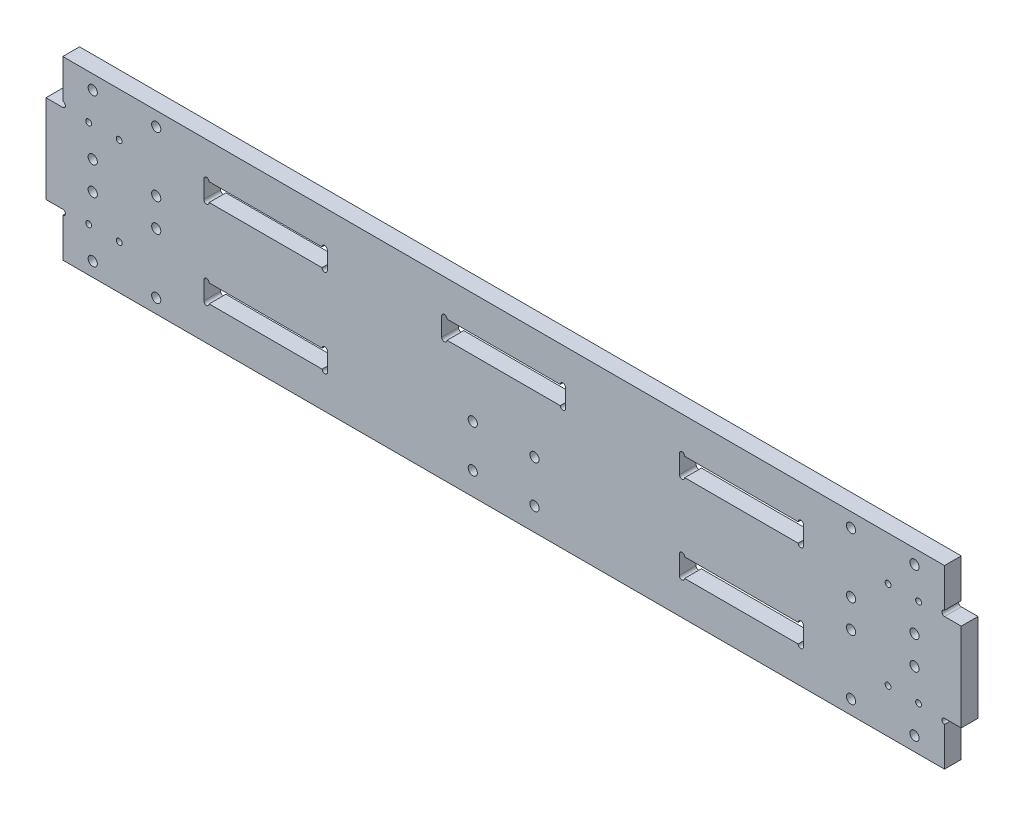
SolidWorks part; units mm, degrees
ref_plane "Front Plane" through (0, 0, 0) normal (0, 0, 1) x (1, 0, 0)
ref_plane "Top Plane" through (0, 0, 0) normal (0, 1, 0) x (1, 0, 0)
ref_plane "Right Plane" through (0, 0, 0) normal (1, 0, 0) x (0, 0, -1)
sketch "Sketch1" plane through (0, 0, 0) normal (0, 0, 1) x (1, 0, 0)
  line L0 (-250, -25) -> (-259.5, -25)
  line L1 (-250, 50) -> (250, 50)
  line L2 (-250, 50) -> (-250, 25)
  line L3 (-250, -50) -> (250, -50)
  line L4 (250, 50) -> (250, 25)
  line L5 (-250, 50) -> (250, -50) construction
  line L6 (-250, -50) -> (250, 50) construction
  line L7 (-259.5, -25) -> (-259.5, 25)
  line L8 (-259.5, 25) -> (-250, 25)
  line L9 (-250, -25) -> (-250, -50)
  line L10 (0, 50) -> (0, -50) construction
  line L11 (250, -25) -> (259.5, -25)
  line L12 (259.5, -25) -> (259.5, 25)
  line L13 (259.5, 25) -> (250, 25)
  line L14 (250, -25) -> (250, -50)
  line L15 (-259.5, 0) -> (258.3936, 0) construction
  line L17 (-170, 19.8) -> (-100, 19.8)
  line L18 (-170, 19.8) -> (-170, 30)
  line L19 (-170, 30) -> (-100, 30)
  line L20 (-100, 19.8) -> (-100, 30)
  line L21 (-170, 19.8) -> (-100, 30) construction
  line L22 (-170, 30) -> (-100, 19.8) construction
  line L23 (-99.9, -30) -> (-170, -30)
  line L24 (-99.9, -30) -> (-99.9, -19.7)
  line L25 (-99.9, -19.7) -> (-170, -19.7)
  line L26 (-170, -30) -> (-170, -19.7)
  line L27 (-99.9, -30) -> (-170, -19.7) construction
  line L28 (-99.9, -19.7) -> (-170, -30) construction
  line L29 (35.1, 30) -> (-35.1, 30)
  line L30 (35.1, 30) -> (35.1, 19.6)
  line L31 (35.1, 19.6) -> (-35.1, 19.6)
  line L32 (-35.1, 30) -> (-35.1, 19.6)
  line L33 (35.1, 30) -> (-35.1, 19.6) construction
  line L34 (35.1, 19.6) -> (-35.1, 30) construction
  line L35 (170, 30) -> (99.7, 30)
  line L36 (170, 30) -> (170, 19.5)
  line L37 (170, 19.5) -> (99.7, 19.5)
  line L38 (99.7, 30) -> (99.7, 19.5)
  line L39 (170, 30) -> (99.7, 19.5) construction
  line L40 (170, 19.5) -> (99.7, 30) construction
  line L41 (170, -30) -> (99.6, -30)
  line L42 (170, -30) -> (170, -19.4)
  line L43 (170, -19.4) -> (99.6, -19.4)
  line L44 (99.6, -30) -> (99.6, -19.4)
  line L45 (170, -30) -> (99.6, -19.4) construction
  line L46 (170, -19.4) -> (99.6, -30) construction
  circle A0 centre (-233, -42) radius 2.6
  circle A1 centre (-197, -42) radius 2.6
  circle A2 centre (-197, -8) radius 2.6
  circle A3 centre (-233, -8) radius 2.6
  circle A4 centre (-197, 42) radius 2.6
  circle A5 centre (-197, 8) radius 2.6
  circle A6 centre (-233, 8) radius 2.6
  circle A7 centre (-233, 42) radius 2.6
  circle A8 centre (233, 42) radius 2.6
  circle A9 centre (233, 8) radius 2.6
  circle A10 centre (197, 8) radius 2.6
  circle A11 centre (197, 42) radius 2.6
  circle A12 centre (233, -8) radius 2.6
  circle A13 centre (197, -8) radius 2.6
  circle A14 centre (197, -42) radius 2.6
  circle A15 centre (233, -42) radius 2.6
  circle A16 centre (-17.5, -37) radius 2.6
  circle A17 centre (17.5, -37) radius 2.6
  circle A18 centre (17.5, -13) radius 2.6
  circle A19 centre (-17.5, -13) radius 2.6
  point P0 (0, 0)
  point P52 (-135, 24.9)
  point P63 (-134.95, -24.85)
  point P68 (0, 24.8)
  point P73 (124, 24.8)
  point P78 (123.75, -24.75)
  dimension "D5" = 5.2
  dimension "D9" = 8
  dimension "D10" = 5.2
  dimension "D14" = 70
  dimension "D15" = 10.2
  dimension "D17" = 10.3
  dimension "D18" = 70.2
  dimension "D1" = 500
  dimension "D2" = 100
  dimension "D3" = 50
  dimension "D4" = 9.5
  dimension "D8" = 17
  dimension "D13" = 13
  dimension "D16" = 70.1
  dimension "D19" = 10.4
  dimension "D20" = 70.3
  dimension "D21" = 10.5
  dimension "D22" = 70.4
  dimension "D23" = 10.6
  dimension "D24" = 80
  dimension "D25" = 20
  dimension "D26" = 20
  dimension "D27" = 20
  dimension "D28" = 20
  dimension "D29" = 20
  dimension "D30" = 80
  dimension "D6" = 2
  dimension "D7" = 2
  dimension "D11" = 2
  dimension "D12" = 2
extrude "Boss-Extrude1" add sketch "Sketch1" along normal blind 9.5
hole_wizard "Ø3.3 (3.3) Diameter Hole1" positions "Sketch2" profile "Sketch3" hole size "Ø3.3" standard "ISO" end condition through all
sketch "Sketch2" plane through (0, 0, 9.5) normal (0, 0, 1) x (1, 0, 0)
  line L0 (-250, 25) -> (-259.5, 25) construction
  line L1 (-250, 50) -> (-250, 25) construction
  line L2 (-259.5, 0) -> (259.5, 0) construction
  line L3 (-259.5, 25) -> (-259.5, -25) construction
  line L4 (259.5, -25) -> (259.5, 25) construction
  line L6 (0, 50) -> (0, -50) construction
  line L7 (250, 50) -> (-250, 50) construction
  line L8 (-250, -50) -> (250, -50) construction
  point P0 (-235.3, 25)
  point P2 (-218, 25)
  point P32 (-218, -25)
  point P33 (-235.3, -25)
  point P40 (235.3, -25)
  point P41 (218, -25)
  point P42 (218, 25)
  point P43 (235.3, 25)
  dimension "D1" = 17.3
  dimension "D2" = 0
  dimension "D3" = 0
  dimension "D4" = 14.7
sketch "Sketch3" plane through (-235.3, 25, 9.5) normal (1, 0, 0) x (0, -1, 0)
  line L0 (0, 0) -> (0, 9.5)
  line L1 (0, 9.5) -> (1.65, 9.5)
  line L2 (1.65, 9.5) -> (1.65, 0)
  line L5 (1.65, 0) -> (0, 0)
  line L11 (0, -6.35) -> (0, 107.95) construction
  dimension "Thru Hole Dia." = 3.3
  dimension "Thru Hole Depth" = 9.5
sketch3d "3DSketch1"
  line L0 (-99.9, -19.7, 9.5) -> (-170, -19.7, 9.5) construction
  point P0 (-133.6754, -19.7, 9.5)
hole_wizard "Ø3.0 (3) Diameter Hole1" positions "Sketch4" profile "Sketch5" hole size "Ø3.0" standard "ISO" end condition through all
sketch "Sketch4" plane through (0, 0, 9.5) normal (0, 0, 1) x (1, 0, 0)
  line L0 (-250, 50) -> (-250, 25) construction
  line L1 (-250, -25) -> (-250, -50) construction
  line L2 (-100, 30) -> (-170, 30) construction
  line L3 (-170, 19.8) -> (-100, 19.8) construction
  line L4 (-99.9, -19.7) -> (-170, -19.7) construction
  line L5 (-170, -30) -> (-99.9, -30) construction
  line L6 (35.1, 30) -> (-35.1, 30) construction
  line L7 (-35.1, 19.6) -> (35.1, 19.6) construction
  line L8 (170, 30) -> (99.7, 30) construction
  line L9 (99.7, 19.5) -> (170, 19.5) construction
  line L10 (170, -19.4) -> (99.6, -19.4) construction
  line L11 (99.6, -30) -> (170, -30) construction
  line L12 (250, 25) -> (250, 50) construction
  line L13 (250, -50) -> (250, -25) construction
  line L15 (170, 19.5) -> (170, 30) construction
  line L16 (99.7, 30) -> (99.7, 19.5) construction
  line L17 (99.6, -19.4) -> (99.6, -30) construction
  line L18 (170, -30) -> (170, -19.4) construction
  line L19 (-35.1, 30) -> (-35.1, 19.6) construction
  line L20 (35.1, 19.6) -> (35.1, 30) construction
  line L21 (-170, 30) -> (-170, 19.8) construction
  line L22 (-100, 19.8) -> (-100, 30) construction
  line L23 (-170, -19.7) -> (-170, -30) construction
  line L24 (-99.9, -30) -> (-99.9, -19.7) construction
  line L25 (-250, 25) -> (-259.5, 25) construction
  line L26 (-259.5, -25) -> (-250, -25) construction
  point P0 (-250, 26.5)
  point P4 (-250, -26.5)
  point P8 (-168.5, 30)
  point P12 (-101.5, 30)
  point P14 (-101.5, 19.8)
  point P18 (-168.5, 19.8)
  point P20 (-168.5, -19.7)
  point P24 (-168.5, -30)
  point P28 (-101.4, -19.7)
  point P30 (-101.4, -30)
  point P32 (-33.6, 30)
  point P36 (-33.6, 19.6)
  point P40 (33.6, 30)
  point P42 (33.6, 19.6)
  point P44 (168.5, 30)
  point P48 (168.5, 19.5)
  point P52 (101.2, 30)
  point P54 (101.2, 19.5)
  point P56 (101.1, -19.4)
  point P60 (101.1, -30)
  point P64 (168.5, -19.4)
  point P66 (168.5, -30)
  point P68 (250, 26.5)
  point P72 (250, -26.5)
  point P79 (0, 0)
  point P81 (0, 0)
  point P85 (0, 0)
  point P86 (0, 0)
  point P94 (0, 0)
  point P95 (0, 0)
  point P96 (0, 0)
  point P101 (0, 0)
  point P102 (0, 0)
  point P107 (0, 0)
  point P108 (0, 0)
  point P109 (0, 0)
  point P110 (0, 0)
  point P119 (168.5, -19.4)
  dimension "D1" = 1.5
  dimension "D2" = 1.5
  dimension "D3" = 1.5
  dimension "D4" = 1.5
  dimension "D5" = 1.5
  dimension "D6" = 1.5
  dimension "D7" = 1.5
  dimension "D8" = 1.5
  dimension "D9" = 1.5
  dimension "D10" = 1.5
  dimension "D11" = 1.5
  dimension "D12" = 1.5
  dimension "D13" = 1.5
  dimension "D14" = 1.5
sketch "Sketch5" plane through (-250, 26.5, 9.5) normal (1, 0, 0) x (0, -1, 0)
  line L0 (0, 0) -> (0, 9.5)
  line L1 (0, 9.5) -> (1.5, 9.5)
  line L2 (1.5, 9.5) -> (1.5, 0)
  line L5 (1.5, 0) -> (0, 0)
  line L11 (0, -6.35) -> (0, 107.95) construction
  dimension "Thru Hole Dia." = 3
  dimension "Thru Hole Depth" = 9.5
